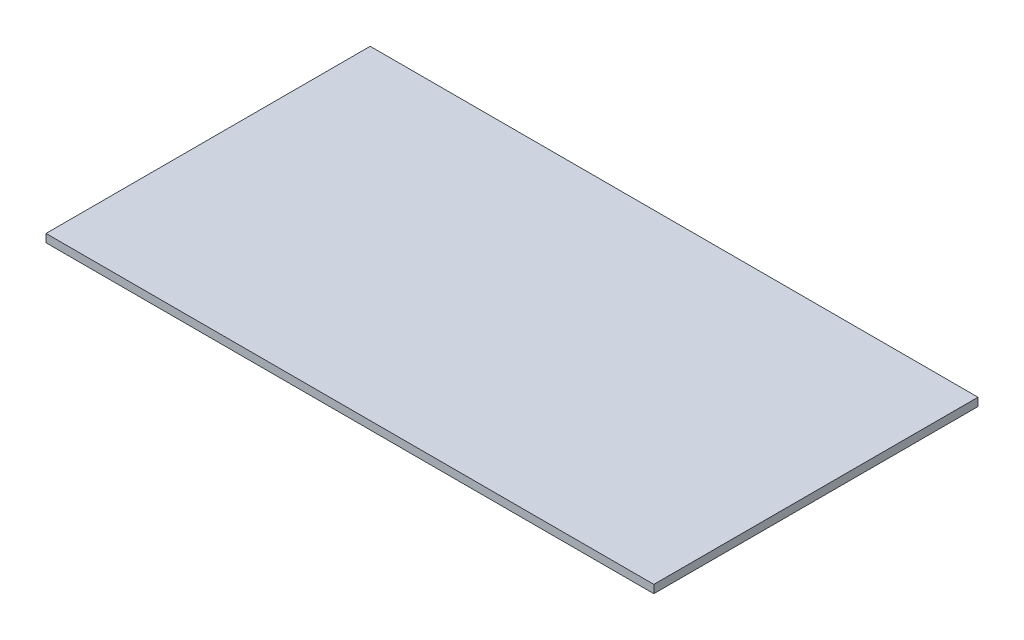
SolidWorks part; units mm, degrees
ref_plane "Alzado" through (0, 0, 0) normal (0, 0, 1) x (1, 0, 0)
ref_plane "Planta" through (0, 0, 0) normal (0, 1, 0) x (1, 0, 0)
ref_plane "Vista lateral" through (0, 0, 0) normal (1, 0, 0) x (0, 0, -1)
sketch "Croquis1" plane through (0, 0, 0) normal (0, 1, 0) x (1, 0, 0)
  line L1 (750, -400) -> (-750, -400)
  line L2 (750, -400) -> (750, 400)
  line L3 (750, 400) -> (-750, 400)
  line L4 (-750, -400) -> (-750, 400)
  line L5 (750, -400) -> (-750, 400) construction
  line L6 (750, 400) -> (-750, -400) construction
  point P0 (0, 0)
  dimension "D1" = 1500
  dimension "D2" = 800
extrude "Saliente-Extruir1" add sketch "Croquis1" along normal blind 20
sketch "Croquis2" plane through (0, 20, 0) normal (0, 1, 0) x (1, 0, 0)
  line L0 (-250, 400) -> (-250, -400) construction
  line L1 (750, 400) -> (-750, 400) construction
  line L2 (-750, -400) -> (750, -400) construction
  line L3 (250, 400) -> (250, -400) construction
  line L4 (-250, 0) -> (250, 0) construction
  point P10 (0, 0)
  dimension "D1" = 500
